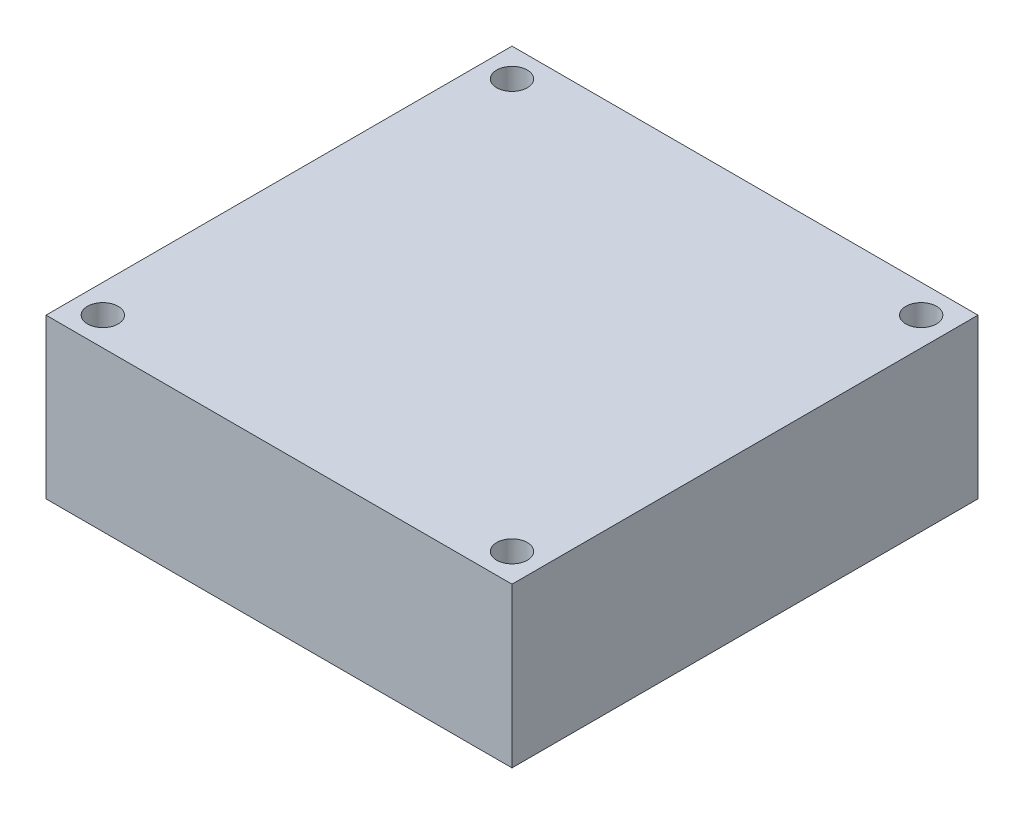
SolidWorks part; units mm, degrees
ref_plane "前视基准面" through (0, 0, 0) normal (0, 0, 1) x (1, 0, 0)
ref_plane "上视基准面" through (0, 0, 0) normal (0, 1, 0) x (1, 0, 0)
ref_plane "右视基准面" through (0, 0, 0) normal (1, 0, 0) x (0, 0, -1)
sketch "草图1" plane through (0, 0, 0) normal (0, 1, 0) x (1, 0, 0)
  line L1 (-20.5, -20.5) -> (20.5, -20.5)
  line L2 (-20.5, -20.5) -> (-20.5, 20.5)
  line L3 (-20.5, 20.5) -> (20.5, 20.5)
  line L4 (20.5, -20.5) -> (20.5, 20.5)
  line L5 (-20.5, -20.5) -> (20.5, 20.5) construction
  line L6 (-20.5, 20.5) -> (20.5, -20.5) construction
  point P0 (0, 0)
  dimension "D1" = 41
  dimension "D2" = 41
extrude "凸台-拉伸1" add sketch "草图1" along normal blind 14 contours L4 L3 L2 L1
sketch "草图2" plane through (0, 14, 0) normal (0, 1, 0) x (1, 0, 0)
  line L1 (-18, -18) -> (18, -18)
  line L2 (-18, -18) -> (-18, 18)
  line L3 (-18, 18) -> (18, 18)
  line L4 (18, -18) -> (18, 18)
  line L5 (-18, -18) -> (18, 18) construction
  line L6 (-18, 18) -> (18, -18) construction
  circle A0 centre (-18, 18) radius 1.35
  circle A1 centre (18, 18) radius 1.35
  circle A2 centre (18, -18) radius 1.35
  circle A3 centre (-18, -18) radius 1.35
  point P0 (0, 0)
  point P16 (0, 0)
  dimension "D3" = 2.7
  dimension "D1" = 36
  dimension "D2" = 36
  dimension "D4" = 4
extrude "切除-拉伸1" cut sketch "草图2" against normal blind 14 contours A0 | A1 | A2 | A3
